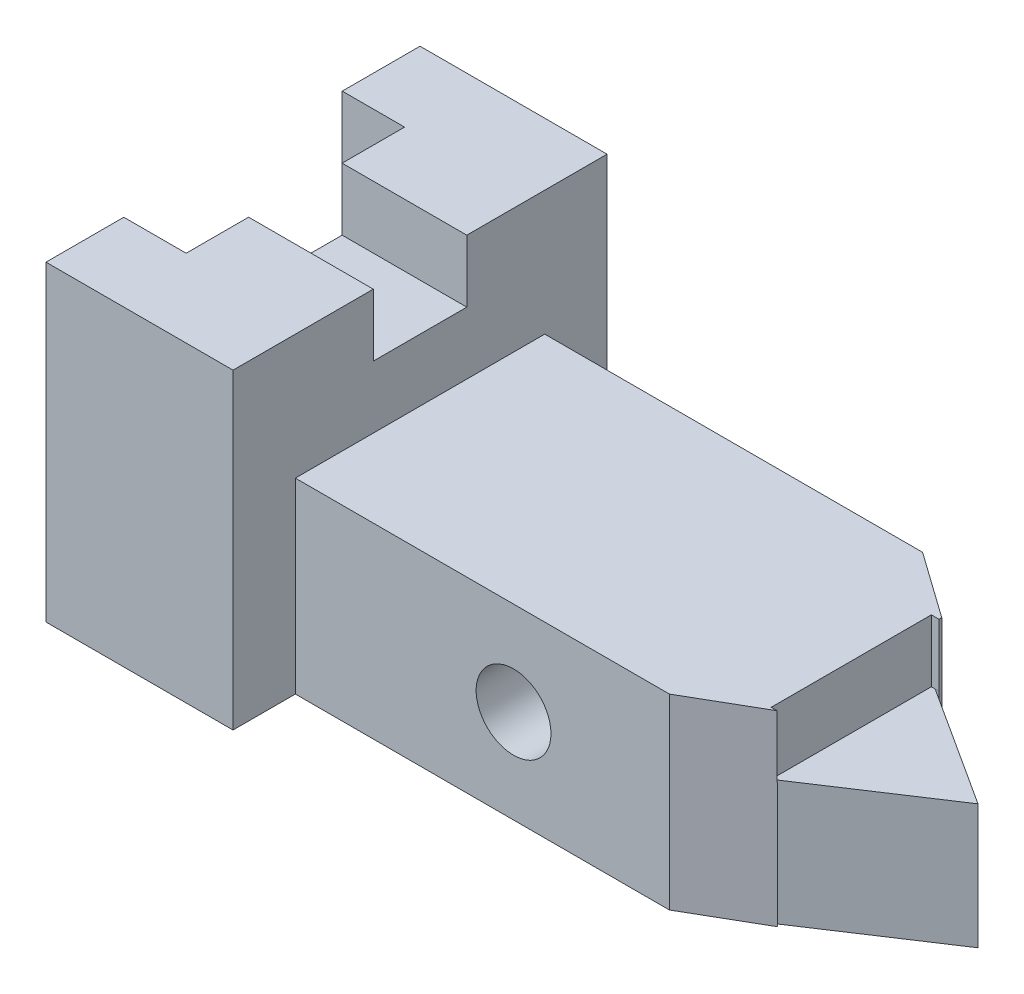
SolidWorks part; units mm, degrees
ref_plane "Front Plane" through (0, 0, 0) normal (0, 0, 1) x (1, 0, 0)
ref_plane "Top Plane" through (0, 0, 0) normal (0, 1, 0) x (1, 0, 0)
ref_plane "Right Plane" through (0, 0, 0) normal (1, 0, 0) x (0, 0, -1)
sketch "Sketch1" plane through (0, 0, 0) normal (0, 0, 1) x (1, 0, 0)
  line L1 (-21.8341, -16.8122) -> (8.1659, -16.8122)
  line L2 (-21.8341, -16.8122) -> (-21.8341, 33.1878)
  line L3 (-21.8341, 33.1878) -> (8.1659, 33.1878)
  line L4 (8.1659, -16.8122) -> (8.1659, 33.1878)
  dimension "D1" = 50
  dimension "D2" = 30
extrude "Boss-Extrude1" add sketch "Sketch1" against normal blind 60
sketch "Sketch2" plane through (8.1659, 0, 0) normal (1, 0, 0) x (0, 0, -1)
  line L0 (0, -16.8122) -> (0, 13.1878) construction
  line L1 (0, -16.8122) -> (0, 33.1878) construction
  line L2 (0, 13.1878) -> (10, 13.1878) construction
  line L3 (60, 13.1878) -> (50, 13.1878) construction
  line L4 (60, -16.8122) -> (60, 33.1878) construction
  line L5 (60, -16.8122) -> (0, -16.8122) construction
  line L6 (10, 13.1878) -> (50, 13.1878)
  line L7 (10, 13.1878) -> (10, -16.8122)
  line L8 (10, -16.8122) -> (50, -16.8122)
  line L9 (50, 13.1878) -> (50, -16.8122)
  dimension "D1" = 30
  dimension "D2" = 10
extrude "Boss-Extrude2" add sketch "Sketch2" along normal blind 90
sketch "Sketch3" plane through (0, 0, -10) normal (0, 0, 1) x (1, 0, 0)
  line L0 (8.1659, -16.8122) -> (8.1659, 13.1878) construction
  line L1 (8.1659, -1.8122) -> (43.1659, -1.8122) construction
  circle A0 centre (43.1659, -1.8122) radius 6
  dimension "D2" = 12
  dimension "D1" = 35
extrude "Cut-Extrude1" cut sketch "Sketch3" against normal blind 90
sketch "Sketch4" plane through (0, 13.1878, 0) normal (0, 1, 0) x (1, 0, 0)
  line L0 (8.1659, 50) -> (79.3893, 50) construction
  line L1 (98.1659, 50) -> (8.1659, 50) construction
  line L2 (98.1659, 50) -> (79.3893, 50) construction
  line L3 (8.1659, 50) -> (43.7776, 50) construction
  line L4 (43.7776, 50) -> (68.7776, 50) construction
  line L5 (79.3893, 50) -> (79.3893, 10) construction
  line L6 (98.1659, 10) -> (8.1659, 10) construction
  line L7 (68.7776, 50) -> (79.3893, 42.4631) construction
  line L8 (68.1659, 10) -> (79.3893, 16.4798) construction
  line L9 (68.7776, 50) -> (79.3893, 42.4631)
  line L10 (79.3893, 42.4631) -> (79.3893, 16.4798)
  line L11 (79.3893, 16.4798) -> (68.1659, 10)
  line L12 (68.1659, 10) -> (79.3893, 10)
  line L13 (79.3893, 10) -> (79.3893, 16.4798)
  line L14 (68.7776, 50) -> (79.3893, 50)
  line L15 (79.3893, 50) -> (79.3893, 42.4631)
  line M10 (98.1659, 50) -> (8.1659, 50)
  dimension "D1" = 25
extrude "Cut-Extrude3" cut sketch "Sketch4" against normal blind 90 contours L15 L9 M10 | L11 L12 L13
sketch "Sketch5" plane through (98.1659, 0, 0) normal (1, 0, 0) x (0, 0, -1)
sketch "Sketch6" plane through (98.1659, 0, 0) normal (1, 0, 0) x (0, 0, -1)
  line L0 (50, 13.1878) -> (10, 13.1878) construction
  line L1 (12.1673, 42.837) -> (16.3244, 13.1878) construction
  line L2 (16.3244, 13.1878) -> (38.6819, 42.837) construction
  line L3 (38.6819, 42.837) -> (42.0114, 13.1878) construction
  line L5 (16.3244, 13.1878) -> (42.0114, 13.1878)
  line L6 (16.3244, 13.1878) -> (16.3244, 3.1878)
  line L7 (16.3244, 3.1878) -> (42.0114, 3.1878)
  line L8 (42.0114, 13.1878) -> (42.0114, 3.1878)
  point P0 (16.3244, 13.1878)
  point P1 (42.0114, 13.1878)
  dimension "D1" = 10
extrude "Cut-Extrude4" cut sketch "Sketch6" against normal blind 20
sketch "Sketch7" plane through (0, 0, -10) normal (0, 0, 1) x (1, 0, 0)
  line L1 (79.3893, 13.1878) -> (98.1659, 13.1878)
  line L2 (79.3893, 13.1878) -> (79.3893, -16.8122)
  line L3 (79.3893, -16.8122) -> (98.1659, -16.8122)
  line L4 (98.1659, 13.1878) -> (98.1659, -16.8122)
extrude "Cut-Extrude5" cut sketch "Sketch7" against normal blind 6
sketch "Sketch8" plane through (0, 0, -16) normal (0, 0, 1) x (1, 0, 0)
  line L1 (79.3893, 13.1878) -> (98.1659, 13.1878)
  line L2 (79.3893, 13.1878) -> (79.3893, -16.8122)
  line L3 (79.3893, -16.8122) -> (98.1659, -16.8122)
  line L4 (98.1659, 13.1878) -> (98.1659, -16.8122)
extrude "Cut-Extrude6" cut sketch "Sketch8" against normal blind 1
sketch "Sketch9" plane through (0, 0, -50) normal (0, 0, -1) x (-1, 0, 0)
  line L0 (-79.3893, -16.8122) -> (-68.7776, -16.8122) construction
  line L1 (-98.1659, 13.1878) -> (-79.3893, 13.1878)
  line L2 (-98.1659, 13.1878) -> (-98.1659, -16.8122)
  line L3 (-98.1659, -16.8122) -> (-79.3893, -16.8122)
  line L4 (-79.3893, 13.1878) -> (-79.3893, -16.8122)
  line L5 (-79.3893, -16.8122) -> (-79.3893, 13.1878) construction
extrude "Cut-Extrude7" cut sketch "Sketch9" against normal blind 8
sketch "Sketch10" plane through (0, 3.1878, 0) normal (0, 1, 0) x (1, 0, 0)
  line L0 (78.7776, 42.0114) -> (98.1659, 29.5)
  line L1 (78.1659, 42.0114) -> (79.3893, 42.0114) construction
  line L2 (98.1659, 17) -> (98.1659, 42) construction
  line L3 (98.1659, 29.5) -> (78.1659, 16.3244)
  line L4 (78.1659, 16.3244) -> (78.1659, 42.0114)
  line L5 (78.1659, 16.3244) -> (98.1659, 17)
  line L6 (98.1659, 17) -> (98.1659, 29.5)
  line L7 (78.7776, 42.0114) -> (98.1659, 42)
  line L8 (98.1659, 42) -> (98.1659, 29.5)
  line M1 (98.1659, 42) -> (79.3893, 42)
  line M2 (79.3893, 42) -> (79.3893, 42.0114)
  line M6 (79.1201, 16.3244) -> (79.3893, 16.4798)
  line M7 (79.3893, 16.4798) -> (79.3893, 17)
  line M8 (79.3893, 17) -> (98.1659, 17)
  line M9 (98.1659, 17) -> (98.1659, 42)
extrude "Cut-Extrude8" cut sketch "Sketch10" against normal blind 48 contours L3 L5 M6 M7 M8 M9 | L7 L0 M9 M1 M2
sketch "Sketch11" plane through (0, 33.1878, 0) normal (0, 1, 0) x (1, 0, 0)
  line L0 (-21.8341, 60) -> (-21.8341, 47.5)
  line L1 (-21.8341, 60) -> (-21.8341, 0) construction
  line L2 (-21.8341, 60) -> (-11.8341, 60)
  line L3 (8.1659, 60) -> (-21.8341, 60) construction
  line L4 (-11.8341, 60) -> (8.1659, 60)
  line L5 (8.1659, 60) -> (8.1659, 37.5)
  line L6 (8.1659, 50) -> (8.1659, 10) construction
  line L7 (8.1659, 37.5) -> (-11.8341, 37.5)
  line L8 (-11.8341, 37.5) -> (-11.8341, 47.5)
  line L9 (-11.8341, 47.5) -> (-21.8341, 47.5)
  line L10 (-21.8341, 0) -> (8.1659, 0)
  line L11 (8.1659, 0) -> (8.1659, 22.5)
  line L12 (8.1659, 60) -> (8.1659, 0) construction
  line L13 (8.1659, 22.5) -> (-11.8341, 22.5)
  line L14 (-11.8341, 22.5) -> (-11.8341, 12.5)
  line L15 (-11.8341, 12.5) -> (-21.8341, 12.5)
  line L16 (-21.8341, 12.5) -> (-21.8341, 0)
  line L18 (-21.8341, 47.5) -> (-11.8341, 47.5)
  line L19 (-21.8341, 47.5) -> (-21.8341, 12.5)
  line L20 (-21.8341, 12.5) -> (-11.8341, 12.5)
  line L21 (-11.8341, 47.5) -> (-11.8341, 12.5)
  line L22 (-11.8341, 37.5) -> (8.1659, 37.5)
  line L23 (-11.8341, 37.5) -> (-11.8341, 22.5)
  line L24 (-11.8341, 22.5) -> (8.1659, 22.5)
  line L25 (8.1659, 37.5) -> (8.1659, 22.5)
  line M11 (8.1659, 0) -> (8.1659, 60)
  dimension "D1" = 12.5
  dimension "D2" = 10
  dimension "D3" = 22.5
extrude "Cut-Extrude9" cut sketch "Sketch11" against normal blind 10 contours L7 L21 L13 M11
sketch "Sketch12" plane through (0, 33.1878, 0) normal (0, 1, 0) x (1, 0, 0)
  line L0 (-21.8341, 47.5197) -> (-21.8341, 12.4803)
  line L1 (-21.8341, 60) -> (-21.8341, 0) construction
  line L2 (-21.8341, 47.5197) -> (-11.8341, 47.5197)
  line L4 (-11.8341, 47.5197) -> (-11.8341, 12.4803)
  line L5 (-11.8341, 12.4803) -> (-21.8341, 12.4803)
  point P5 (-21.8341, 30)
  dimension "D1" = 10
extrude "Cut-Extrude10" cut sketch "Sketch12" against normal blind 70
